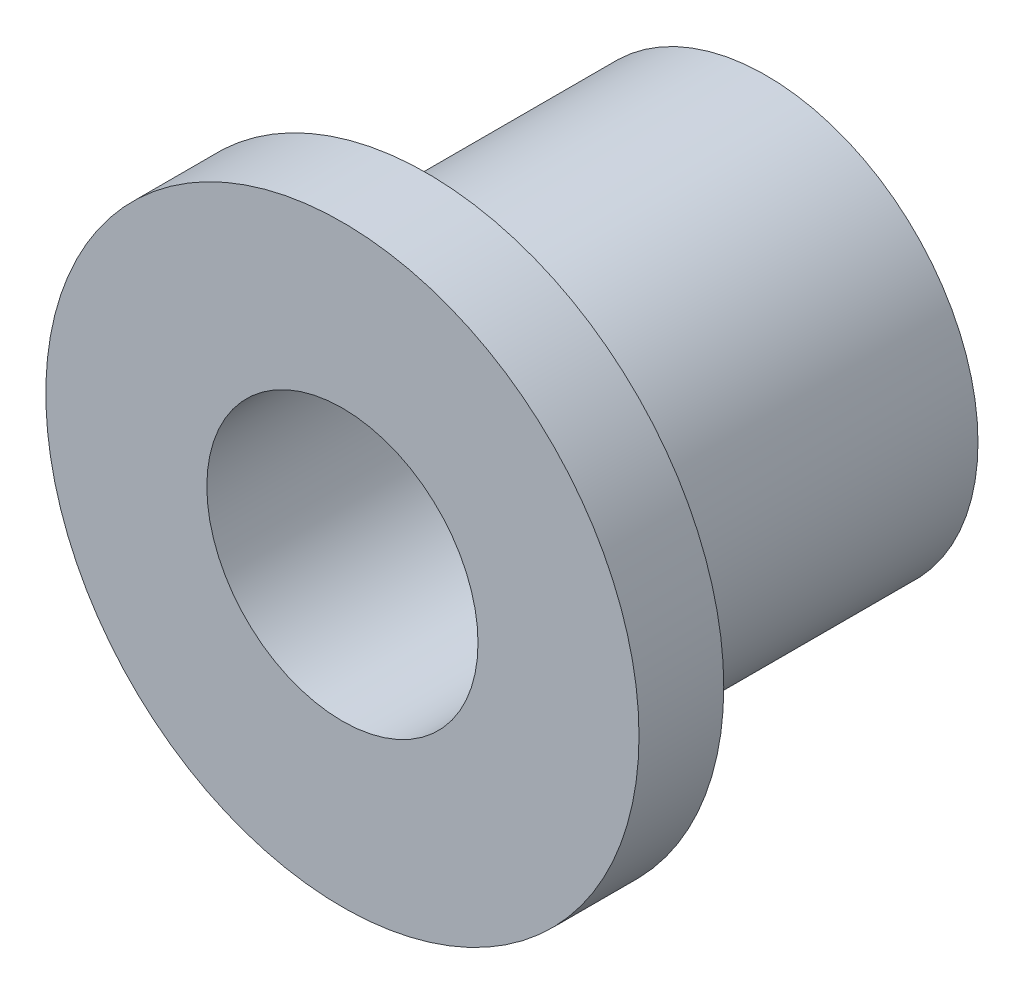
SolidWorks part; units mm, degrees
ref_plane "前视基准面" through (0, 0, 0) normal (0, 0, 1) x (1, 0, 0)
ref_plane "上视基准面" through (0, 0, 0) normal (0, 1, 0) x (1, 0, 0)
ref_plane "右视基准面" through (0, 0, 0) normal (1, 0, 0) x (0, 0, -1)
sketch "草图1" plane through (0, 0, 0) normal (0, 0, 1) x (1, 0, 0)
  circle A0 centre (0, 0) radius 1.6
  circle A1 centre (0, 0) radius 2.5
extrude "凸台-拉伸1" add sketch "草图1" along normal blind 4
sketch "草图2" plane through (0, 0, 4) normal (0, 0, 1) x (1, 0, 0)
  circle A0 centre (0, 0) radius 1.6
  circle A1 centre (0, 0) radius 3.5
extrude "凸台-拉伸2" add sketch "草图2" along normal blind 1
